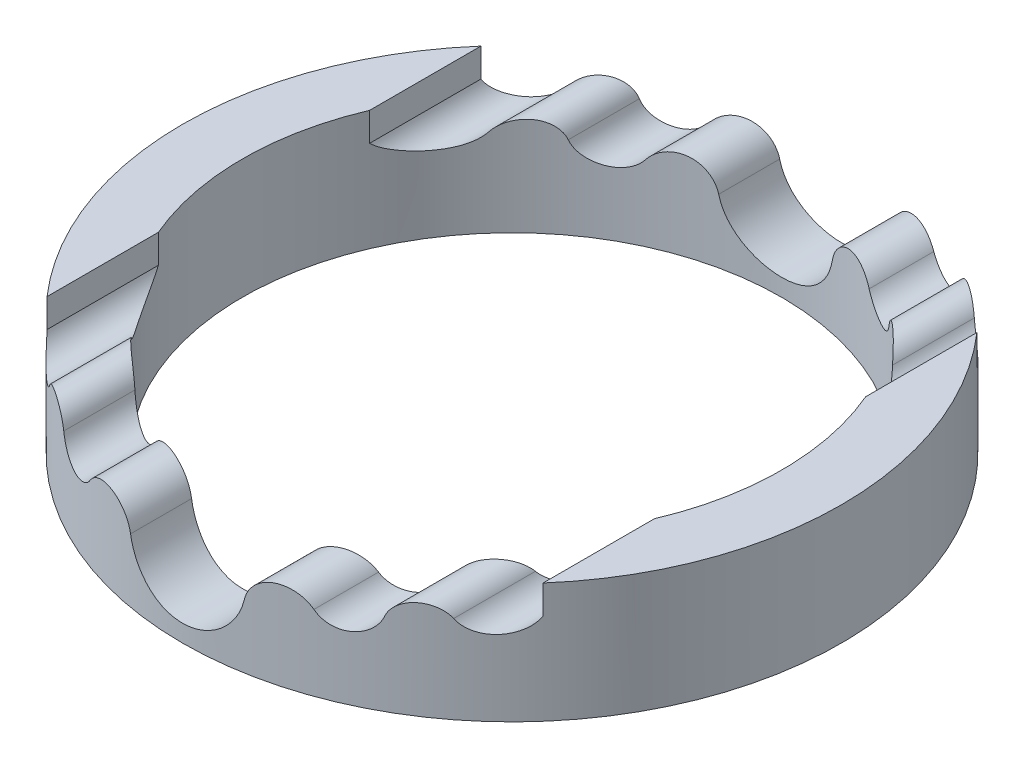
SolidWorks part; units mm, degrees
ref_plane "Front Plane" through (0, 0, 0) normal (0, 0, 1) x (1, 0, 0)
ref_plane "Top Plane" through (0, 0, 0) normal (0, 1, 0) x (1, 0, 0)
ref_plane "Right Plane" through (0, 0, 0) normal (1, 0, 0) x (0, 0, -1)
sketch "Sketch1" plane through (0, 0, 0) normal (0, 1, 0) x (1, 0, 0)
  circle A0 centre (0, 0) radius 27.5
  circle A1 centre (0, 0) radius 22.5
  dimension "D1" = 55
  dimension "D2" = 5
extrude "Boss-Extrude1" add sketch "Sketch1" along normal mid plane 10
sketch "Sketch3" plane through (0, 0, 0) normal (0, 0, 1) x (1, 0, 0)
  line L2 (0, -3.5607) -> (0, 5)
  line L3 (22.5, 5) -> (-22.5, 5) construction
  line L4 (20.7005, 5) -> (-20.7005, 5)
  line L5 (-20.7005, 2.615) -> (-20.7005, 5)
  line L6 (20.7005, 2.615) -> (20.7005, 5)
  arc A0 (-20.7005, 2.615) -> (-16.8561, 2.3204) centre (-18.7001, 3.4879) ccw
  arc A1 (-16.8561, 2.3204) -> (-13.3889, 1.8936) centre (-15.2235, 1.2867) cw
  arc A2 (-13.3889, 1.8936) -> (-9.3349, 1.2867) centre (-11.2085, 2.615) ccw
  arc A3 (-9.3349, 1.2867) -> (-4.7475, 0.3183) centre (-7.2509, -0.1908) cw
  arc A4 (-4.7475, 0.3183) -> (4.7475, 0.3183) centre (0, 1.2839) ccw
  arc A6 (9.3349, 1.2867) -> (4.7475, 0.3183) centre (7.2509, -0.1908) ccw
  arc A7 (13.3889, 1.8936) -> (9.3349, 1.2867) centre (11.2085, 2.615) cw
  arc A8 (16.8561, 2.3204) -> (13.3889, 1.8936) centre (15.2235, 1.2867) ccw
  arc A9 (20.7005, 2.615) -> (16.8561, 2.3204) centre (18.7001, 3.4879) cw
extrude "Cut-Extrude3" cut sketch "Sketch3" against normal through all both and the other way through all contours A3 A4 L2 L4 L5 A0 A1 A2 | A9 L6 L4 L2 A4 A6 A7 A8
